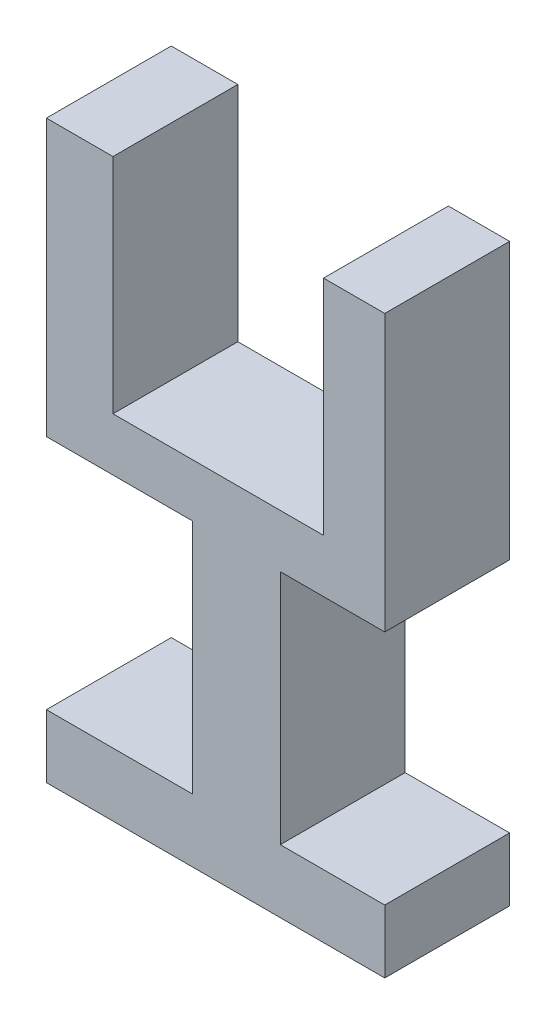
SolidWorks part; units mm, degrees
ref_plane "Front Plane" through (0, 0, 0) normal (0, 0, 1) x (1, 0, 0)
ref_plane "Top Plane" through (0, 0, 0) normal (0, 1, 0) x (1, 0, 0)
ref_plane "Right Plane" through (0, 0, 0) normal (1, 0, 0) x (0, 0, -1)
sketch "Sketch2" plane through (0, 0, 0) normal (0, 0, 1) x (1, 0, 0)
  line L0 (-37.5243, 34.6871) -> (-37.5243, -15.2843)
  line L1 (-37.5243, -15.2843) -> (9.7014, -15.2843)
  line L2 (9.7014, -15.2843) -> (9.7014, 34.6871)
  line L3 (9.7014, 34.6871) -> (23.4298, 34.6871)
  line L4 (23.4298, 34.6871) -> (23.4298, -27.1822)
  line L5 (23.4298, -27.1822) -> (0, -27.1822)
  line L6 (0, -27.1822) -> (0, -80.2165)
  line L7 (0, -80.2165) -> (23.4298, -80.2165)
  line L8 (23.4298, -80.2165) -> (23.4298, -94.3931)
  line L9 (23.4298, -94.3931) -> (-52.459, -94.3931)
  line L10 (-52.459, -94.3931) -> (-52.459, -80.2165)
  line L11 (-52.459, -80.2165) -> (-19.6426, -80.2165)
  line L12 (-19.6426, -80.2165) -> (-19.6426, -27.1822)
  line L13 (-19.6426, -27.1822) -> (-52.459, -27.1822)
  line L14 (-52.459, -27.1822) -> (-52.459, 34.6871)
  line L15 (-52.459, 34.6871) -> (-37.5243, 34.6871)
extrude "Boss-Extrude1" add sketch "Sketch2" along normal blind 28
